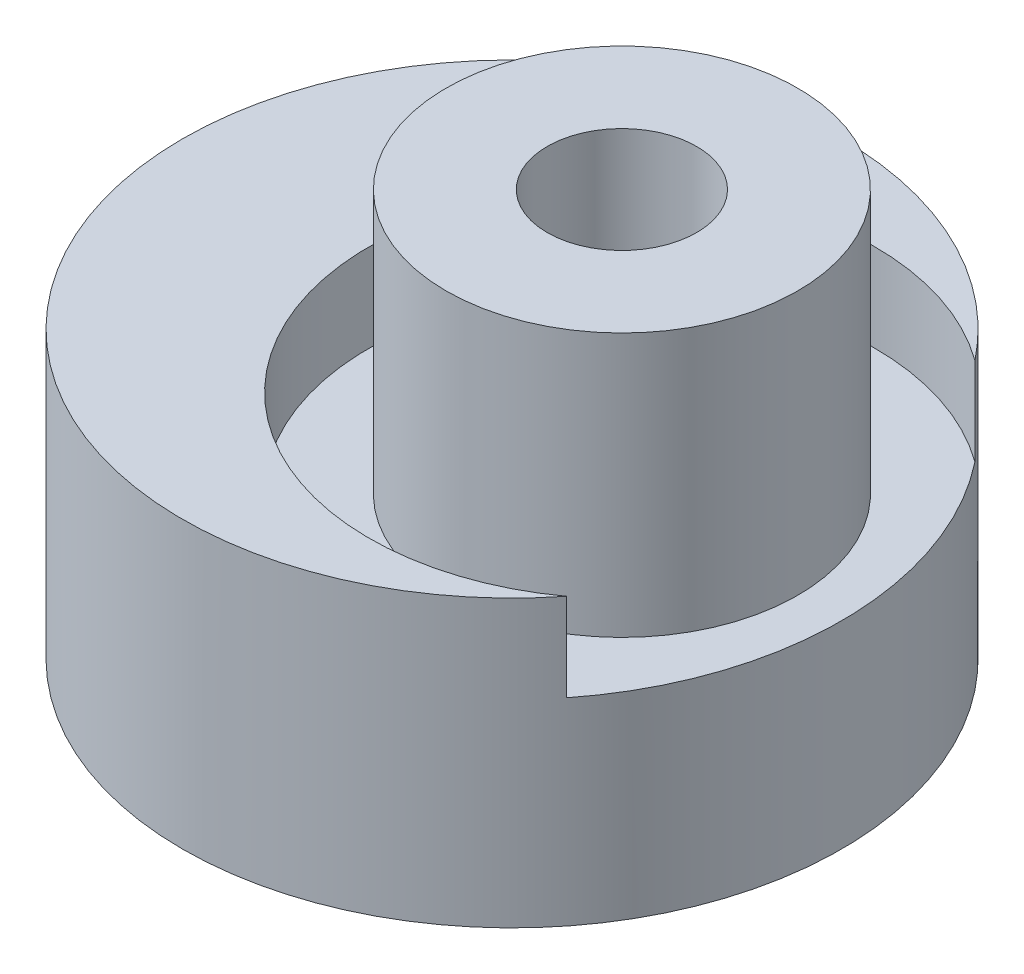
SolidWorks part; units mm, degrees
ref_plane "Спереди" through (0, 0, 0) normal (0, 0, 1) x (1, 0, 0)
ref_plane "Сверху" through (0, 0, 0) normal (0, 1, 0) x (1, 0, 0)
ref_plane "Справа" through (0, 0, 0) normal (1, 0, 0) x (0, 0, -1)
sketch "Эскиз1" plane through (0, 0, 0) normal (0, 1, 0) x (1, 0, 0)
  circle A0 centre (0, 0) radius 3
  circle A1 centre (0, 0) radius 10 construction
  circle A2 centre (-2.5, 0) radius 7.5
  point P4 (5, 0)
  point P5 (10, 0)
  point P6 (-10, 0)
  dimension "D1" = 6
  dimension "D2" = 20
  dimension "D3" = 5
extrude "Бобышка-Вытянуть1" add sketch "Эскиз1" along normal blind 3
sketch "Эскиз2" plane through (0, 3, 0) normal (0, 1, 0) x (1, 0, 0)
  circle A0 centre (-2.5, 0) radius 7.5
  circle A1 centre (0, 0) radius 1.8
  dimension "D1" = 3.6
extrude "Бобышка-Вытянуть2" add sketch "Эскиз2" along normal blind 3.5
sketch "Эскиз3" plane through (0, 6.5, 0) normal (0, 1, 0) x (1, 0, 0)
  circle A1 centre (0, 0) radius 4
  circle A2 centre (0, 0) radius 5.75
  dimension "D1" = 8
  dimension "D2" = 11.5
extrude "Вырез-Вытянуть1" cut sketch "Эскиз3" against normal blind 2
sketch "Эскиз4" plane through (0, 6.5, 0) normal (0, 1, 0) x (1, 0, 0)
  circle A0 centre (0, 0) radius 1.7
  circle A1 centre (0, 0) radius 4
  dimension "D1" = 8
extrude "Бобышка-Вытянуть3" add sketch "Эскиз4" along normal blind 4
sketch "Эскиз5" plane through (0, 0, 0) normal (0, -1, 0) x (1, 0, 0)
  circle A0 centre (0, 0) radius 3
extrude "Вырез-Вытянуть2" cut sketch "Эскиз5" against normal blind 3.5
chamfer "Фаска1" distance 0.6 angle 45 1 edges at (0, 0, 3)
